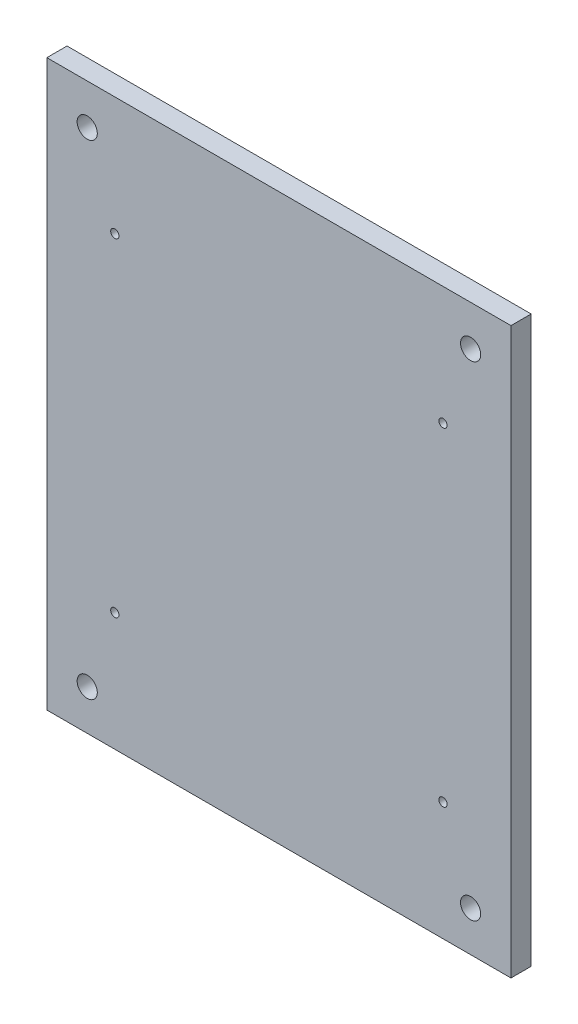
SolidWorks part; units mm, degrees
ref_plane "Front Plane" through (0, 0, 0) normal (0, 0, 1) x (1, 0, 0)
ref_plane "Top Plane" through (0, 0, 0) normal (0, 1, 0) x (1, 0, 0)
ref_plane "Right Plane" through (0, 0, 0) normal (1, 0, 0) x (0, 0, -1)
sketch "Sketch1" plane through (0, 0, 0) normal (0, 0, 1) x (1, 0, 0)
  line L1 (4, 0) -> (90.5, 0)
  line L2 (0, 4) -> (0, 90.5)
  line L3 (4, 94.5) -> (90.5, 94.5)
  line L4 (94.5, 4) -> (94.5, 90.5)
  arc A0 (4, 0) -> (0, 4) centre (4, 4) cw
  arc A1 (90.5, 0) -> (94.5, 4) centre (90.5, 4) ccw
  arc A2 (90.5, 94.5) -> (94.5, 90.5) centre (90.5, 90.5) cw
  arc A3 (0, 90.5) -> (4, 94.5) centre (4, 90.5) cw
  circle A4 centre (6.59, 87.91) radius 1.025
  circle A5 centre (87.91, 87.91) radius 1.025
  circle A6 centre (6.59, 6.59) radius 1.025
  circle A7 centre (87.91, 6.59) radius 1.025
  point P7 (0, 0)
  point P12 (94.5, 94.5)
  point P15 (0, 94.5)
  point P24 (0, 0)
  point P25 (0, 0)
  point P26 (0, 0)
  point P27 (13.9425, 21.206)
  point P28 (0, 0)
  dimension "D3" = 4
  dimension "D4" = 2.05
  dimension "D1" = 94.5
  dimension "D2" = 94.5
  dimension "D5" = 81.32
  dimension "D6" = 81.32
  dimension "D7" = 6.59
  dimension "D8" = 6.59
extrude "Boss-Extrude1" add sketch "Sketch1" along normal blind 5
sketch "Sketch2" plane through (0, 0, 5) normal (0, 0, 1) x (1, 0, 0)
  line L0 (90.5, 94.5) -> (4, 94.5) construction
  line L5 (-0.25, 107.25) -> (-0.25, -12.75) construction
  line L6 (0, 90.5) -> (0, 4) construction
  line L8 (-10.25, 117.25) -> (104.75, 117.25)
  line L9 (-10.25, 117.25) -> (-10.25, -22.75)
  line L10 (-10.25, -22.75) -> (104.75, -22.75)
  line L11 (104.75, 117.25) -> (104.75, -22.75)
  circle A0 centre (94.75, 107.25) radius 2.5
  circle A1 centre (94.75, -12.75) radius 2.5
  circle A2 centre (-0.25, 107.25) radius 2.5
  circle A3 centre (-0.25, -12.75) radius 2.5
  point P10 (47.25, 94.5)
  point P18 (0, 47.25)
  point P19 (-0.25, 47.25)
  dimension "D1" = 5
  dimension "D2" = 95
  dimension "D8" = 10
  dimension "D3" = 47.5
  dimension "D4" = 120
  dimension "D5" = 10
  dimension "D6" = 10
  dimension "D7" = 10
extrude "Boss-Extrude2" add sketch "Sketch2" along normal blind 5
sketch "Sketch3" plane through (0, 0, 0) normal (0, 0, -1) x (-1, 0, 0)
  circle A0 centre (-87.91, 6.59) radius 1.025 construction
  circle A1 centre (-6.59, 6.59) radius 1.025 construction
  circle A2 centre (-6.59, 87.91) radius 1.025 construction
  circle A3 centre (-87.91, 87.91) radius 1.025 construction
  circle A4 centre (-87.91, 6.59) radius 1.025
  circle A5 centre (-6.59, 6.59) radius 1.025
  circle A6 centre (-6.59, 87.91) radius 1.025
  circle A7 centre (-87.91, 87.91) radius 1.025
extrude "Cut-Extrude1" cut sketch "Sketch3" along normal up to next from surface
